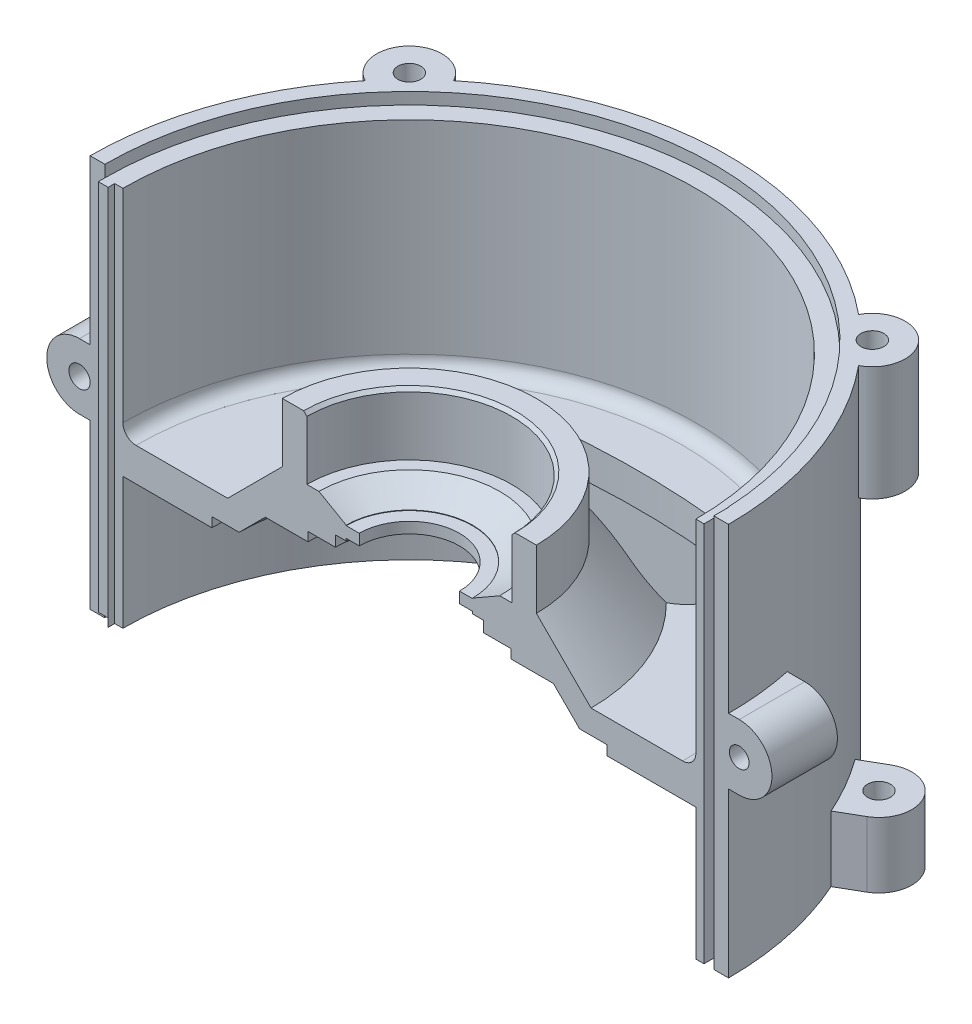
SolidWorks part; units mm, degrees
ref_plane "Plano frontal" through (0, 0, 0) normal (0, 0, 1) x (1, 0, 0)
ref_plane "Plano superior" through (0, 0, 0) normal (0, 1, 0) x (1, 0, 0)
ref_plane "Plano direito" through (0, 0, 0) normal (1, 0, 0) x (0, 0, -1)
sketch "Esboço3" plane through (0, 0, 0) normal (0, 0, 1) x (1, 0, 0)
  line L2 (97.5, 79.8) -> (97.5, 11.3045)
  line L4 (87.5, 0) -> (60.3424, 0)
  line L5 (31.3, 25.96) -> (27.6265, 25.96)
  line L6 (60.3424, 0) -> (60.3424, 2.95)
  line L7 (60.3424, 2.95) -> (52, 2.95)
  line L8 (52, 2.95) -> (44, 10.95)
  line L9 (44, 10.95) -> (31, 10.95)
  line L10 (31, 10.95) -> (31, 13.7)
  line L11 (31, 13.7) -> (22.6, 13.7)
  line L12 (22.6, 13.7) -> (22.6, 17)
  line L13 (22.6, 17) -> (19.3, 17)
  line L14 (19.3, 17) -> (19.3, 17.7)
  line L15 (19.3, 17.7) -> (15.3, 17.7)
  line L16 (15.3, 17.7) -> (15.3, 21.05)
  line L17 (15.3, 21.05) -> (19.3, 21.05)
  line L18 (97.5, 79.8) -> (93, 79.8)
  line L19 (93, 79.8) -> (93, 76.2)
  line L20 (93, 76.2) -> (87.5, 76.2)
  line L21 (87.5, 76.2) -> (87.5, 14.2)
  line L22 (83.5, 10.2) -> (55.5, 10.2)
  line L23 (55.5, 10.2) -> (38.8, 26.9)
  line L24 (38.8, 26.9) -> (38.8, 44.96)
  line L25 (38.8, 44.96) -> (32.3, 44.96)
  line L26 (32.3, 44.96) -> (31.3, 43.96)
  line L27 (31.3, 43.96) -> (31.3, 25.96)
  line L29 (19.3, 21.05) -> (19.3, 21.2)
  line L30 (55, 0) -> (-55, 0) construction
  line L31 (27.6265, 25.96) -> (19.3, 21.2)
  line L33 (97.5, 0) -> (97.5, 11.3045)
  line L34 (97.5, 0) -> (97.5, -40.2)
  line L35 (97.5, -40.2) -> (87.5, -40.2)
  line L36 (87.5, -40.2) -> (87.5, 0)
  arc A1 (87.5, 14.2) -> (83.5, 10.2) centre (83.5, 14.2) cw
  dimension "D32" = 79.8
  dimension "D2" = 7.5
  dimension "D3" = 135
  dimension "D4" = 19
  dimension "D5" = 120
  dimension "D6" = 0.15
  dimension "D7" = 135
  dimension "D8" = 16
  dimension "D9" = 34.84
  dimension "D10" = 28
  dimension "D11" = 66
  dimension "D12" = 3.6
  dimension "D13" = 93
  dimension "D14" = 10
  dimension "D15" = 17.7
  dimension "D16" = 1
  dimension "D17" = 31.3
  dimension "D18" = 10
  dimension "D19" = 52
  dimension "D20" = 44
  dimension "D21" = 135
  dimension "D22" = 31
  dimension "D23" = 22.6
  dimension "D24" = 19.3
  dimension "D25" = 15.3
  dimension "D26" = 2.75
  dimension "D27" = 3.3
  dimension "D28" = 0.7
  dimension "D29" = 3.35
  dimension "D31" = 97.5
ref_axis "Eixo1" through (0, -3.3221, 0) along (0, 1, 0)
revolve "Revolução2" add sketch "Esboço3" angle 180 about axis through (0, -3.3221, 0) along (0, 1, 0)
sketch "Esboço4" plane through (0, 79.8, 0) normal (0, 1, 0) x (1, 0, 0)
  line L0 (70.71, 70.71) -> (-70.71, 70.71) construction
  line L1 (-70.71, 70.71) -> (-70.71, -70.71) construction
  line L2 (-70.71, -70.71) -> (70.71, -70.71) construction
  line L3 (70.71, -70.71) -> (70.71, 70.71) construction
  line L4 (-55, 0) -> (55, 0) construction
  line L5 (0, -55) -> (0, 55) construction
  circle A0 centre (70.71, 70.71) radius 10
  circle A3 centre (-70.71, 70.71) radius 10
  point P0 (70.71, 0)
  point P8 (0, -70.71)
  dimension "D2" = 20
  dimension "D1" = 141.42
extrude "Ressalto-extrusão1" add sketch "Esboço4" against normal blind 35
sketch "Esboço5" plane through (0, -40.2, 0) normal (0, -1, 0) x (1, 0, 0)
  line L0 (0, 0) -> (70.71, -70.71) construction
  line L1 (0, 0) -> (0, -105) construction
  line L2 (10, -105) -> (10, -96.9858)
  line L3 (-10, -105) -> (-10, -96.9858)
  line L4 (10, -96.9858) -> (-10, -96.9858)
  arc A1 (10, -105) -> (-10, -105) centre (0, -105) cw
  arc A3 (-97.5, 0) -> (97.5, 0) centre (0, 0) ccw construction
  dimension "D2" = 10
  dimension "D1" = 105
extrude "Ressalto-extrusão2" add sketch "Esboço5" against normal blind 20
sketch "Esboço8" plane through (0, -40.2, 0) normal (0, -1, 0) x (1, 0, 0)
  circle A0 centre (0, -105) radius 3.5
  dimension "D1" = 7
extrude "Corte-extrusão2" cut sketch "Esboço8" against normal blind 20
pattern_circular "PadrãoCircular1" count 6 over 360 about axis through (0, 0, 0) along (0, 1, 0) of "Ressalto-extrusão2", "Corte-extrusão2"
sketch "Esboço6" plane through (0, 79.8, 0) normal (0, 1, 0) x (1, 0, 0)
  circle A2 centre (70.71, 70.71) radius 3.5
  circle A3 centre (-70.71, 70.71) radius 3.5
  dimension "D1" = 7
extrude "Corte-extrusão1" cut sketch "Esboço6" against normal blind 15
sketch "Esboço9" plane through (0, 13.7, 0) normal (0, -1, 0) x (1, 0, 0)
  line L0 (0, 0) -> (18.7383, -18.7383) construction
  line L1 (-18.7383, -18.7383) -> (0, 0) construction
  line L2 (-18.7383, -18.7383) -> (18.7383, -18.7383) construction
  circle A2 centre (18.7383, -18.7383) radius 1.25
  circle A3 centre (-18.7383, -18.7383) radius 1.25
  point P13 (4.0879, -3.0957)
  dimension "D2" = 26.5
  dimension "D1" = 26.5
extrude "Corte-extrusão3" cut sketch "Esboço9" against normal blind 6
sketch "Esboço10" plane through (0, 0, 0) normal (0, 0, 1) x (1, 0, 0)
  line L0 (93, -40.2) -> (93, 79.8)
  line L2 (97.5, 79.8) -> (93, 79.8) construction
  line L3 (93, 79.8) -> (90, 79.8)
  line L4 (93, 79.8) -> (70.4477, 79.8) construction
  line L5 (90, 79.8) -> (90, -40.2)
  line L6 (90, -40.2) -> (93, -40.2)
  line L7 (87.5, -40.2) -> (97.5, -40.2) construction
  dimension "D1" = 3
extrude "Corte-extrusão4" cut sketch "Esboço10" against normal blind 4.5
sketch "Esboço11" plane through (0, 0, 0) normal (0, 0, 1) x (1, 0, 0)
  line L0 (-90, -40.2) -> (-90, 76.2)
  line L2 (-87.5, -40.2) -> (-97.5, -40.2) construction
  line L3 (-90, 76.2) -> (-93, 76.2)
  line L4 (-93, 76.2) -> (-93, -40.2)
  line L5 (-93, -40.2) -> (-90, -40.2)
  line L6 (-93, 79.8) -> (-93, 76.2) construction
  line L7 (-93, 76.2) -> (-87.5, 76.2) construction
  dimension "D1" = 3
extrude "Ressalto-extrusão5" add sketch "Esboço11" along normal blind 2
sketch "Esboço12" plane through (0, 0, 0) normal (0, 0, 1) x (1, 0, 0)
  line L0 (-124.1305, 19.8) -> (136.9824, 19.8) construction
  line L2 (-97.5, -40.2) -> (-97.5, 79.8) construction
  line L3 (-100.75, 9.8) -> (-100.75, 29.8) construction
  line L4 (-100.75, 29.8) -> (-87.5, 29.8)
  line L5 (-87.5, 76.2) -> (-87.5, 14.2) construction
  line L6 (-87.5, 29.8) -> (-87.5, 9.8)
  line L7 (-87.5, 9.8) -> (-100.75, 9.8)
  arc A1 (-100.75, 9.8) -> (-100.75, 29.8) centre (-100.75, 19.8) cw
  circle A2 centre (-100.75, 19.8) radius 3.25
  point P8 (-97.5, 19.8)
  dimension "D2" = 6.5
  dimension "D1" = 20
extrude "Ressalto-extrusão6" add sketch "Esboço12" against normal blind 20
sketch "Esboço13" plane through (0, 0, 0) normal (0, 0, 1) x (1, 0, 0)
  line L0 (100.75, 29.8) -> (100.75, 9.8) construction
  line L3 (-100.75, 19.8) -> (140.3594, 19.8) construction
  line L4 (100.75, 29.8) -> (93, 29.8)
  line L5 (93, 29.8) -> (93, 9.8)
  line L6 (93, 9.8) -> (100.75, 9.8)
  line L7 (93, -40.2) -> (93, 79.8) construction
  line L8 (97.5, -40.2) -> (97.5, 79.8) construction
  arc A0 (100.75, 9.8) -> (100.75, 29.8) centre (100.75, 19.8) ccw
  circle A1 centre (100.75, 19.8) radius 3
  dimension "D3" = 6
  dimension "D1" = 20
  dimension "D2" = 3.25
extrude "Ressalto-extrusão7" add sketch "Esboço13" against normal blind 20
sketch "Esboço14" plane through (0, 0, 0) normal (0, -1, 0) x (-1, 0, 0)
  line L0 (0, -185) -> (0, 115) construction
  arc A0 (32.1753, 52.6546) -> (-32.1753, 52.6546) centre (0, -166.8724) ccw construction
  arc A1 (34.3505, 67.4961) -> (-34.3505, 67.4961) centre (0, -166.8724) ccw
  arc A2 (30, 37.8132) -> (-30, 37.8132) centre (0, -166.8724) ccw
  arc A3 (30, 37.8132) -> (34.3505, 67.4961) centre (32.1753, 52.6546) ccw
  arc A4 (-34.3505, 67.4961) -> (-30, 37.8132) centre (-32.1753, 52.6546) ccw
  arc A5 (10, 105) -> (-10, 105) centre (0, 105) ccw construction
  point P3 (0, 55)
  dimension "D1" = 30
  dimension "D2" = 300
  dimension "D3" = 55
  dimension "D4" = 60
extrude "Corte-extrusão5" cut sketch "Esboço14" against normal through all
sketch "Esboço16" plane through (0, 76.2, 0) normal (0, 1, 0) x (1, 0, 0)
  circle A0 centre (0, 0) radius 93
extrude "Corte-extrusão6" cut sketch "Esboço16" along normal blind 10
sketch "Esboço17" plane through (0, -40.2, 0) normal (0, -1, 0) x (1, 0, 0)
  circle A0 centre (0, 0) radius 93.1124
  circle A1 centre (0, 0) radius 90.1124
  dimension "D1" = 3
extrude "Corte-extrusão7" cut sketch "Esboço17" against normal blind 2.5
ref_plane "Plano1" through (0, -20.1, 0) normal (0, -1, 0) x (-1, 0, 0)
sketch "Esboço18" plane through (0, -20.1, 0) normal (0, -1, 0) x (-1, 0, 0)
  line L0 (0, 0) -> (0, 115) construction
  line L1 (50, 81.2817) -> (-50, 81.2817)
  line L2 (50, 81.2817) -> (50, 64.043)
  line L3 (50, 64.043) -> (-50, 64.043)
  line L4 (-50, 81.2817) -> (-50, 64.043)
  line L5 (50, 81.2817) -> (-50, 64.043) construction
  line L6 (50, 64.043) -> (-50, 81.2817) construction
  arc A0 (10, 105) -> (-10, 105) centre (0, 105) ccw construction
  point P0 (0, 72.6623)
  point P11 (0, 77.0034)
  point P12 (0, 0)
  dimension "D1" = 100
extrude "Corte-extrusão8" cut sketch "Esboço18" against normal mid plane 30
sketch "Esboço19" plane through (0, -20.1, 0) normal (0, -1, 0) x (-1, 0, 0)
  line L0 (32.3966, 81.2817) -> (-32.3966, 81.2817)
  arc A0 (32.3966, 81.2817) -> (-32.3966, 81.2817) centre (0, 0) ccw
  arc A1 (87.5, 0) -> (-87.5, 0) centre (0, 0) ccw construction
  point P7 (-32.2413, 81.3434)
extrude "Ressalto-extrusão9" add sketch "Esboço19" along normal mid plane 30
